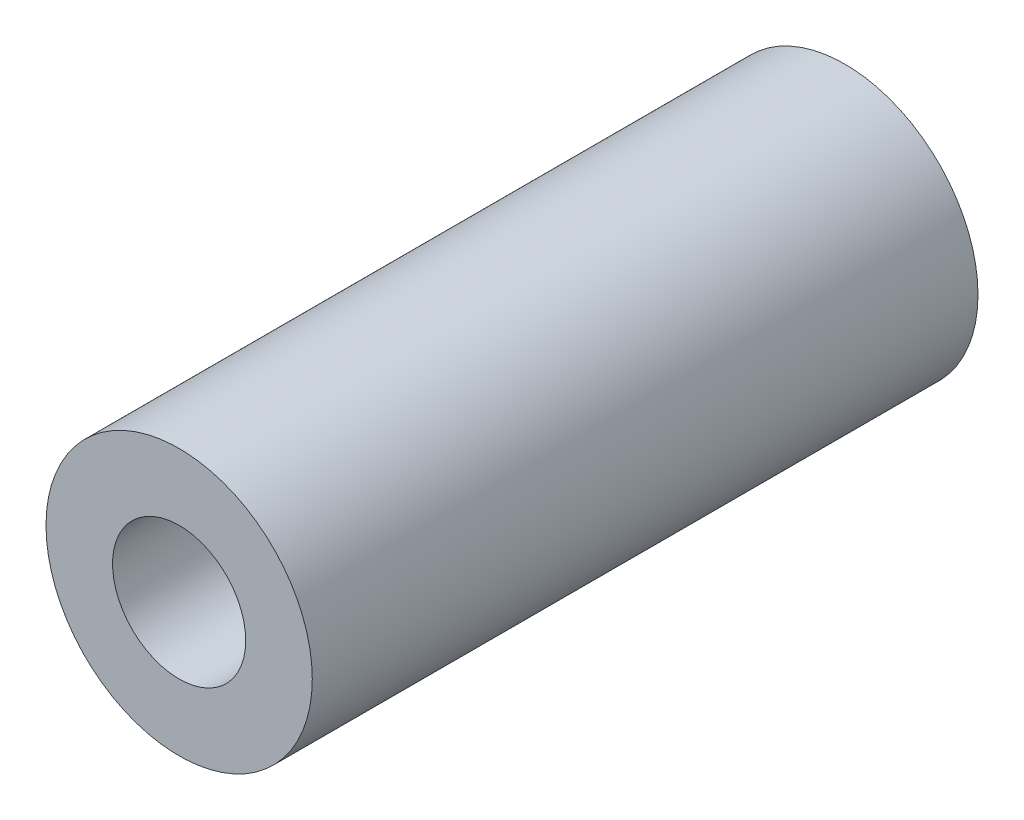
SolidWorks part; units mm, degrees
ref_plane "Front Plane" through (0, 0, 0) normal (0, 0, 1) x (1, 0, 0)
ref_plane "Top Plane" through (0, 0, 0) normal (0, 1, 0) x (1, 0, 0)
ref_plane "Right Plane" through (0, 0, 0) normal (1, 0, 0) x (0, 0, -1)
sketch "Esquisse1" plane through (0, 0, 0) normal (0, 0, 1) x (1, 0, 0)
  circle A0 centre (0, 0) radius 1.5
  circle A1 centre (0, 0) radius 3
  dimension "D1" = 6
  dimension "D2" = 3
extrude "Main" add sketch "Esquisse1" along normal blind 15
